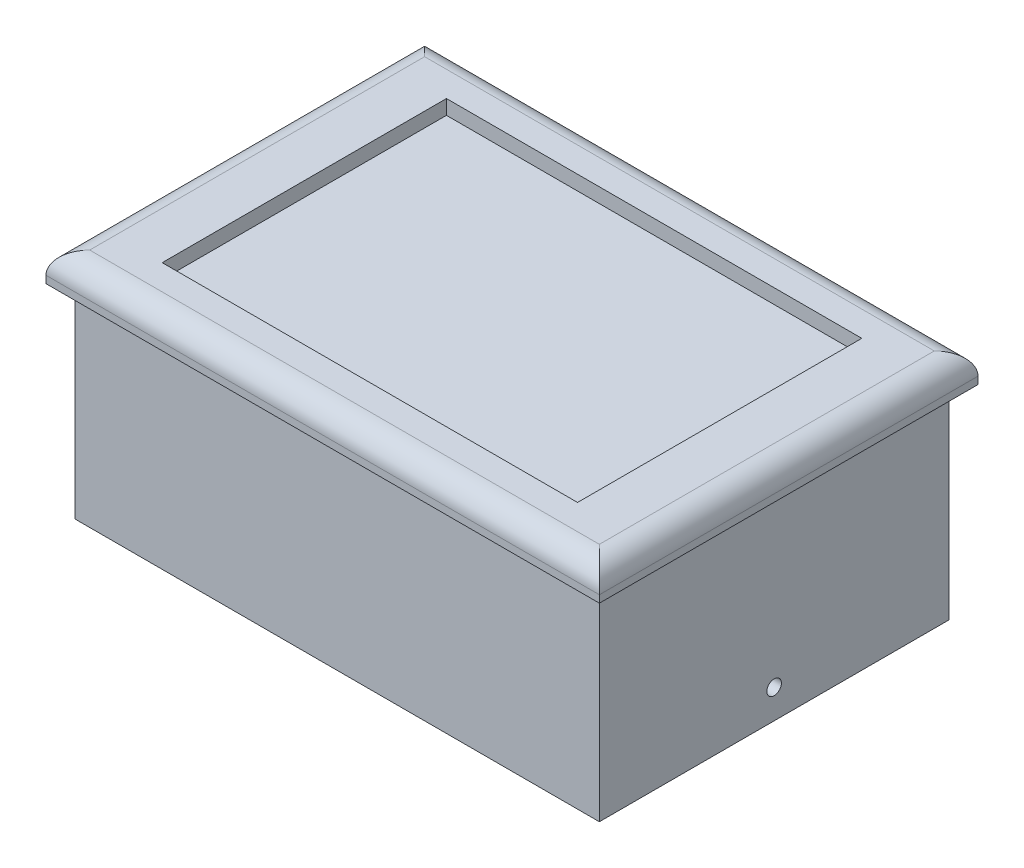
SolidWorks part; units mm, degrees
ref_plane "Front Plane" through (0, 0, 0) normal (0, 0, 1) x (1, 0, 0)
ref_plane "Top Plane" through (0, 0, 0) normal (0, 1, 0) x (1, 0, 0)
ref_plane "Right Plane" through (0, 0, 0) normal (1, 0, 0) x (0, 0, -1)
sketch "Sketch1" plane through (0, 0, 0) normal (0, 1, 0) x (1, 0, 0)
  line L0 (60.325, 41.275) -> (-60.325, 41.275)
  line L1 (57.15, -38.1) -> (-57.15, -38.1) construction
  line L2 (57.15, -38.1) -> (57.15, 38.1) construction
  line L3 (57.15, 38.1) -> (-57.15, 38.1) construction
  line L4 (-57.15, -38.1) -> (-57.15, 38.1) construction
  line L5 (57.15, -38.1) -> (-57.15, 38.1) construction
  line L6 (57.15, 38.1) -> (-57.15, -38.1) construction
  line L7 (-60.325, -41.275) -> (-60.325, 41.275)
  line L8 (60.325, -41.275) -> (-60.325, -41.275)
  line L9 (60.325, -41.275) -> (60.325, 41.275)
  point P0 (0, 0)
  dimension "D1" = 76.2
  dimension "D2" = 114.3
  dimension "D3" = 3.175
extrude "MainBody" add sketch "Sketch1" along normal blind 50.8
sketch "Sketch2" plane through (0, 50.8, 0) normal (0, 1, 0) x (1, 0, 0)
  line L0 (-45.2763, -30.9888) -> (-45.2763, 30.9888)
  line L1 (44.45, -30.1625) -> (-44.45, -30.1625) construction
  line L2 (44.45, -30.1625) -> (44.45, 30.1625) construction
  line L3 (44.45, 30.1625) -> (-44.45, 30.1625) construction
  line L4 (-44.45, -30.1625) -> (-44.45, 30.1625) construction
  line L5 (44.45, -30.1625) -> (-44.45, 30.1625) construction
  line L6 (44.45, 30.1625) -> (-44.45, -30.1625) construction
  line L7 (45.2763, 30.9888) -> (-45.2763, 30.9888)
  line L8 (45.2763, -30.9888) -> (45.2763, 30.9888)
  line L9 (45.2763, -30.9888) -> (-45.2763, -30.9888)
  point P0 (0, 0)
  dimension "D1" = 60.325
  dimension "D2" = 88.9
  dimension "D3" = 0.8263
extrude "SolarPanelRecess" cut sketch "Sketch2" against normal blind 3.175
sketch "Sketch3" plane through (0, 47.625, 0) normal (0, 1, 0) x (1, 0, 0)
  line L16 (38.9263, 24.6388) -> (-38.9263, 24.6388)
  line L17 (-38.9263, 24.6388) -> (-38.9263, -24.6388)
  line L18 (-38.9263, -24.6388) -> (38.9263, -24.6388)
  line L19 (38.9263, -24.6388) -> (38.9263, 24.6388)
  line L20 (38.9263, 24.6388) -> (-38.9263, 24.6388)
  line L21 (-38.9263, 24.6388) -> (-38.9263, -24.6388)
  line L22 (-38.9263, -24.6388) -> (38.9263, -24.6388)
  line L23 (38.9263, -24.6388) -> (38.9263, 24.6388)
  dimension "D1" = 6.35
extrude "SolarPanelWiringRecess" cut sketch "Sketch3" against normal through all
sketch "Sketch4" plane through (0, 0, 0) normal (0, -1, 0) x (1, 0, 0)
  line L0 (-63.5, -44.45) -> (63.5, -44.45)
  line L1 (52.3875, -33.3375) -> (-52.3875, -33.3375)
  line L2 (52.3875, -33.3375) -> (52.3875, 33.3375)
  line L3 (52.3875, 33.3375) -> (-52.3875, 33.3375)
  line L4 (-52.3875, -33.3375) -> (-52.3875, 33.3375)
  line L5 (52.3875, -33.3375) -> (-52.3875, 33.3375) construction
  line L6 (52.3875, 33.3375) -> (-52.3875, -33.3375) construction
  line L7 (-57.15, 38.1) -> (57.15, 38.1)
  line L8 (-57.15, 38.1) -> (-57.15, -38.1)
  line L9 (-57.15, -38.1) -> (57.15, -38.1)
  line L10 (57.15, 38.1) -> (57.15, -38.1)
  line L11 (-57.15, 38.1) -> (57.15, -38.1) construction
  line L12 (-57.15, -38.1) -> (57.15, 38.1) construction
  line L13 (63.5, 44.45) -> (63.5, -44.45)
  line L14 (-63.5, 44.45) -> (63.5, 44.45)
  line L15 (-63.5, 44.45) -> (-63.5, -44.45)
  point P0 (0, 0)
  point P6 (0, 0)
  dimension "D1" = 66.675
  dimension "D2" = 104.775
  dimension "D3" = 114.3
  dimension "D4" = 76.2
  dimension "D5" = 6.35
extrude "InsideEnclosureRecess_OutsideFlange" cut sketch "Sketch4" against normal offset from surface (44.45 mm away) 3.175
fillet "TopFancyFillet" radius 4.7625 4 edges at (60.325, 50.8, 0) (0, 50.8, 41.275) (-60.325, 50.8, 0) (0, 50.8, -41.275)
sketch "Sketch6" plane through (-57.15, 0, 0) normal (-1, 0, 0) x (0, 0, 1)
  line L1 (-14.2875, 25.4) -> (14.2875, 25.4) construction
  line L2 (-14.2875, 24.6063) -> (14.2875, 24.6063)
  line L3 (14.2875, 24.6063) -> (26.9875, 24.6063)
  line L4 (26.9875, 24.6063) -> (26.9875, 11.9063)
  line L5 (26.9875, 11.9063) -> (-23.8125, 11.9062)
  line L6 (-23.8125, 11.9062) -> (-23.8125, 24.6063)
  line L7 (-23.8125, 24.6063) -> (-14.2875, 24.6063)
  dimension "D2" = 6.35
  dimension "D3" = 9.525
  dimension "D4" = 12.7
  dimension "D1" = 0.7937
extrude "CableAccess" cut sketch "Sketch6" against normal up to next
sketch "Sketch9" plane through (57.15, 0, 0) normal (1, 0, 0) x (0, 0, -1)
  line L0 (0, 0) -> (0, 6.35) construction
  line L1 (-38.1, 0) -> (38.1, 0) construction
  circle A0 centre (0, 6.35) radius 1.5875
  dimension "D1" = 3.175
  dimension "D2" = 6.35
extrude "TopEdgeHoles" cut sketch "Sketch9" against normal through all
sketch "Sketch10" plane through (0, 44.45, 0) normal (0, -1, 0) x (1, 0, 0)
  line L0 (-52.3875, 33.3375) -> (-52.3875, -33.3375) construction
  line L1 (50.0062, 31.75) -> (-50.0063, 31.75) construction
  line L2 (50.0062, 31.75) -> (50.0062, -31.75) construction
  line L3 (50.0062, -31.75) -> (-50.0063, -31.75) construction
  line L4 (-50.0063, 31.75) -> (-50.0063, -31.75) construction
  line L5 (50.0062, 31.75) -> (-50.0063, -31.75) construction
  line L6 (50.0062, -31.75) -> (-50.0063, 31.75) construction
  line L7 (-52.3875, 33.3375) -> (52.3875, 33.3375) construction
  line L8 (-52.3875, 33.3375) -> (-52.3875, 23.8125)
  line L9 (-52.3875, 33.3375) -> (-42.8625, 33.3375)
  line L10 (-42.8625, 33.3375) -> (52.3875, 33.3375) construction
  line L11 (-52.3875, 23.8125) -> (-52.3875, -33.3375) construction
  line L12 (-52.3875, -33.3375) -> (52.3875, -33.3375) construction
  arc A0 (-52.3875, 23.8125) -> (-42.8625, 33.3375) centre (-52.3875, 33.3375) ccw
  arc A1 (-42.8625, 33.3375) -> (-52.3875, 23.8125) centre (-52.3875, 33.3375) ccw construction
  circle A2 centre (-52.3875, -33.3375) radius 9.525
  circle A3 centre (52.3875, -33.3375) radius 9.525
  circle A4 centre (52.3875, 33.3375) radius 9.525
  point P0 (0, 0)
  line M12 (52.3875, 33.3375) -> (-52.3875, 33.3375)
  line M13 (-52.3875, 33.3375) -> (-52.3875, -33.3375)
  line M14 (-52.3875, -33.3375) -> (52.3875, -33.3375)
  line M15 (52.3875, -33.3375) -> (52.3875, 33.3375)
  dimension "D3" = 19.05
  dimension "D1" = 63.5
  dimension "D2" = 100.0125
extrude "CornerStandoffs" add sketch "Sketch10" along normal blind 15.875 contours A0 M13 M12 | A4 M12 M15 | A2 M14 M13 | A3 M15 M14
sketch "Sketch11" plane through (0, 28.575, 0) normal (0, -1, 0) x (1, 0, 0)
  line L0 (50.0062, 31.75) -> (-50.0063, 31.75) construction
  line L1 (-50.0063, 31.75) -> (-50.0063, -31.75) construction
  line L2 (50.0062, -31.75) -> (-50.0063, -31.75) construction
  line L3 (50.0062, 31.75) -> (50.0062, -31.75) construction
  line L4 (50.0062, 31.75) -> (-50.0063, 31.75) construction
  line L5 (-50.0063, 31.75) -> (-50.0063, -31.75) construction
  line L6 (50.0062, -31.75) -> (-50.0063, -31.75) construction
  line L7 (50.0062, 31.75) -> (50.0062, -31.75) construction
  line L8 (46.8312, 28.575) -> (46.8312, -28.575) construction
  line L9 (46.8312, -28.575) -> (-46.8313, -28.575) construction
  line L10 (-46.8313, 28.575) -> (-46.8313, -28.575) construction
  line L11 (46.8312, 28.575) -> (-46.8313, 28.575) construction
  circle A0 centre (46.8312, -28.575) radius 1.143
  circle A1 centre (-46.8313, -28.575) radius 1.143
  circle A2 centre (-46.8313, 28.575) radius 1.143
  circle A3 centre (46.8312, 28.575) radius 1.143
  dimension "D2" = 2.286
  dimension "D1" = 3.175
extrude "ScrewStandoffHoles" cut sketch "Sketch11" against normal blind 6.35
sketch "Sketch12" plane through (0, 0, 0) normal (0, -1, 0) x (1, 0, 0)
  line L4 (53.975, -34.925) -> (53.975, 34.925)
  line L5 (53.975, 34.925) -> (-53.975, 34.925)
  line L6 (-53.975, 34.925) -> (-53.975, -34.925)
  line L7 (-53.975, -34.925) -> (53.975, -34.925)
  line L8 (55.5625, -36.5125) -> (55.5625, 36.5125)
  line L9 (55.5625, 36.5125) -> (-55.5625, 36.5125)
  line L10 (-55.5625, 36.5125) -> (-55.5625, -36.5125)
  line L11 (-55.5625, -36.5125) -> (55.5625, -36.5125)
  line L12 (55.5625, -36.5125) -> (55.5625, 36.5125)
  line L13 (55.5625, 36.5125) -> (-55.5625, 36.5125)
  line L14 (-55.5625, 36.5125) -> (-55.5625, -36.5125)
  line L15 (-55.5625, -36.5125) -> (55.5625, -36.5125)
  dimension "D1" = 1.5875
  dimension "D2" = 1.5875
extrude "WeatherSealRecess" cut sketch "Sketch12" against normal blind 3.175
sketch "Sketch13" plane through (0, 47.625, 0) normal (0, 1, 0) x (1, 0, 0)
  line L4 (-45.2763, -30.9888) -> (45.2763, -30.9888)
  line L5 (45.2763, -30.9888) -> (45.2763, 30.9888)
  line L6 (45.2763, 30.9888) -> (-45.2763, 30.9888)
  line L7 (-45.2763, 30.9888) -> (-45.2763, -30.9888)
  line L8 (-45.2763, -30.9888) -> (45.2763, -30.9888)
  line L9 (45.2763, -30.9888) -> (45.2763, 30.9888)
  line L10 (45.2763, 30.9888) -> (-45.2763, 30.9888)
  line L11 (-45.2763, 30.9888) -> (-45.2763, -30.9888)
  dimension "D1" = 0
extrude "BlankInsert_BetterBridging" add sketch "Sketch13" against normal blind 0.125
